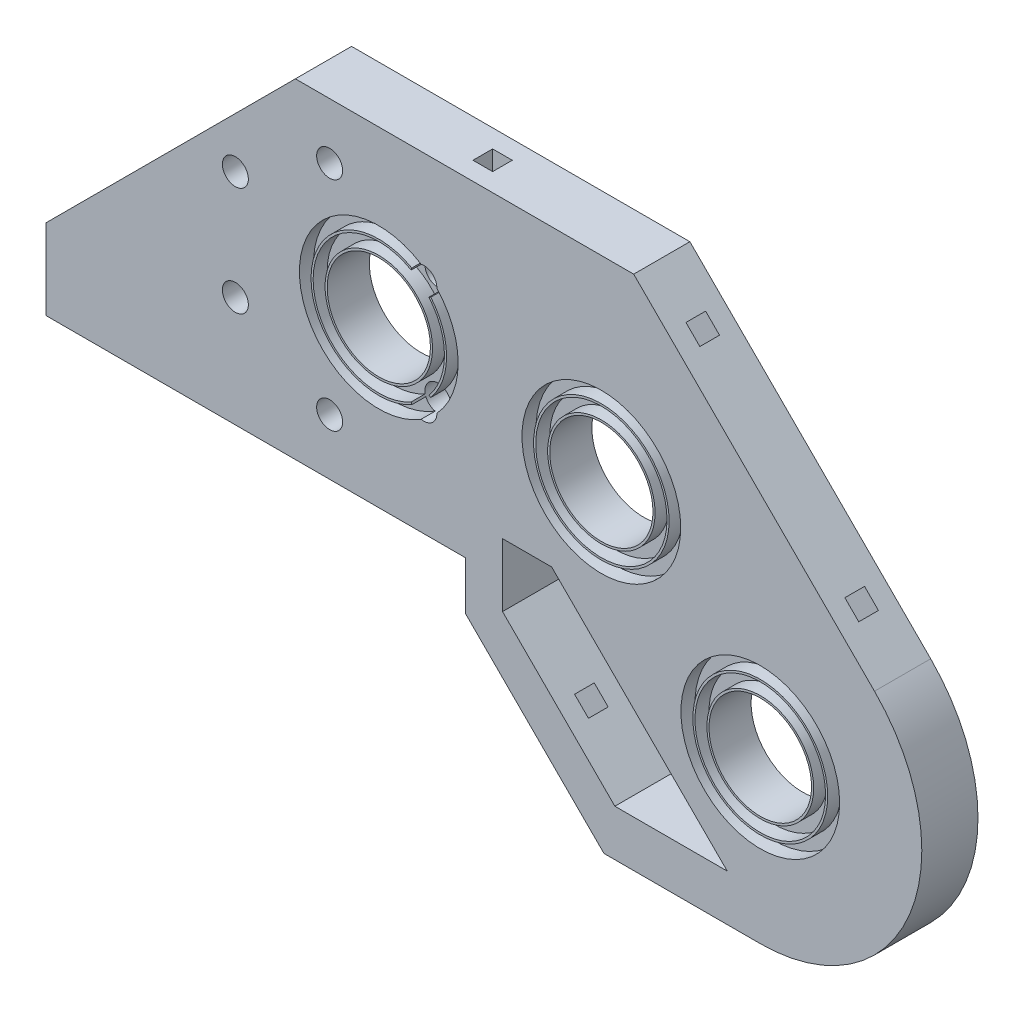
SolidWorks part; units mm, degrees
ref_plane "Plano frontal" through (0, 0, 0) normal (0, 0, 1) x (1, 0, 0)
ref_plane "Plano superior" through (0, 0, 0) normal (0, 1, 0) x (1, 0, 0)
ref_plane "Plano direito" through (0, 0, 0) normal (1, 0, 0) x (0, 0, -1)
sketch "Model" plane through (0, 0, 0) normal (0, 0, 1) x (1, 0, 0)
  line L0 (0, 0) -> (39, 0)
  line L1 (39, 0) -> (39.7, 0)
  line L2 (39.7, 0) -> (39.7, -6.8548)
  line L3 (0, 0) -> (0, 31.4419)
  line L4 (50.1111, 46.949) -> (15.5071, 46.949)
  line L5 (0, 31.4419) -> (15.5071, 46.949)
  line L6 (39.7, -6.8548) -> (52.4452, -19.6)
  line L7 (72, -15) -> (52, 5)
  line L8 (97.9635, 12.6635) -> (63.6779, 46.949)
  line L9 (50.1111, 46.949) -> (63.6779, 46.949)
  line L10 (52.4452, -19.6) -> (59.4452, -26.6)
  line L11 (81.7, -26.6) -> (59.4452, -26.6)
  line L12 (72, -15) -> (77, -20)
  line L13 (52, 5) -> (45, 5)
  line L14 (45, 5) -> (45, -4)
  line L15 (45, -4) -> (61, -20)
  line L16 (61, -20) -> (77, -20)
  circle A2 centre (59.0726, 19.0274) radius 7.35
  arc A5 (81.7, -26.6) -> (97.9635, 12.6635) centre (81.7, -3.6) ccw
  circle A6 centre (81.7, -3.6) radius 7.3
  circle A7 centre (6.9606, 15.731) radius 1.85
  circle A8 centre (6.9606, 31.231) radius 1.85
  circle A9 centre (20.384, 38.981) radius 1.85
  circle A10 centre (33.8074, 31.231) radius 1.85
  circle A11 centre (33.8074, 15.731) radius 1.85
  circle A12 centre (20.384, 7.981) radius 1.85
  circle A13 centre (27.384, 23.481) radius 7.35
sketch "Esboço2" plane through (0, 0, 0) normal (0, 0, 1) x (1, 0, 0)
  circle A15 centre (6.9606, 15.731) radius 3.3
  circle A16 centre (6.9606, 31.231) radius 3.3
  circle A17 centre (33.8074, 15.731) radius 3.3
  circle A18 centre (20.384, 38.981) radius 3.3
  circle A19 centre (33.8074, 31.231) radius 3.3
  circle A20 centre (20.384, 7.981) radius 3.3
sketch "Esboço3" plane through (0, 0, 0) normal (0, 0, 1) x (1, 0, 0)
  circle A3 centre (81.7, -3.6) radius 11.3
  circle A4 centre (59.0726, 19.0274) radius 11.3
  circle A14 centre (27.384, 23.481) radius 11.3
extrude "Ressalto-extrusão1" add sketch "Model" along normal blind 8
sketch "Esboço4" plane through (0, 0, 8) normal (0, 0, 1) x (1, 0, 0)
  circle A3 centre (81.7, -3.6) radius 11.3
  circle A4 centre (59.0726, 19.0274) radius 11.3
  circle A14 centre (27.384, 23.481) radius 11.3
extrude "Corte-extrusão1" cut sketch "Esboço3" along normal blind 2
extrude "Corte-extrusão2" cut sketch "Esboço4" against normal blind 2
extrude "Corte-extrusão4" cut sketch "Esboço2" along normal blind 2
sketch "Esboço7" plane through (55.3135, 55.3135, 0) normal (0.7071, 0.7071, 0) x (0, 0, -1)
  line L0 (0, -36.0727) -> (-8, -36.0727) construction
  line L2 (-4, -52.0727) -> (-4, -20.0727) construction
  line L3 (-5.4, -50.6727) -> (-2.6, -50.6727)
  line L4 (-5.4, -18.6727) -> (-2.6, -18.6727)
  line L5 (-5.4, -18.6727) -> (-5.4, -21.4727)
  line L6 (-5.4, -21.4727) -> (-2.6, -21.4727)
  line L7 (-2.6, -18.6727) -> (-2.6, -21.4727)
  line L8 (-5.4, -18.6727) -> (-2.6, -21.4727) construction
  line L9 (-5.4, -21.4727) -> (-2.6, -18.6727) construction
  line L10 (-2.6, -50.6727) -> (-2.6, -53.4727)
  line L11 (-5.4, -50.6727) -> (-2.6, -53.4727) construction
  line L12 (-5.4, -53.4727) -> (-2.6, -53.4727)
  line L13 (-5.4, -50.6727) -> (-5.4, -53.4727)
  line L14 (-5.4, -53.4727) -> (-2.6, -50.6727) construction
  line L15 (0, -60.3162) -> (0, -11.8291) construction
  line L16 (-8, -60.3162) -> (-8, -11.8291) construction
extrude "Corte-extrusão6" cut sketch "Esboço7" against normal blind 6
sketch "Esboço8" plane through (0, 46.949, 0) normal (0, 1, 0) x (1, 0, 0)
  line L0 (39.5925, 0) -> (39.5925, -8) construction
  line L1 (63.6779, 0) -> (15.5071, 0) construction
  line L2 (63.6779, -8) -> (15.5071, -8) construction
  line L4 (38.1925, -5.4) -> (40.9925, -5.4)
  line L5 (38.1925, -5.4) -> (38.1925, -2.6)
  line L6 (38.1925, -2.6) -> (40.9925, -2.6)
  line L7 (40.9925, -5.4) -> (40.9925, -2.6)
  line L8 (38.1925, -5.4) -> (40.9925, -2.6) construction
  line L9 (38.1925, -2.6) -> (40.9925, -5.4) construction
  point P6 (39.5925, -4)
extrude "Corte-extrusão7" cut sketch "Esboço8" against normal blind 6
sketch "Esboço10" plane through (16.4226, 16.4226, 0) normal (-0.7071, -0.7071, 0) x (0, 0, 1)
  line L0 (0, -46.8812) -> (8, -46.8812) construction
  line L1 (0, -32.9192) -> (0, -60.8431) construction
  line L2 (8, -32.9192) -> (8, -60.8431) construction
  line L4 (2.6, -45.4812) -> (5.4, -45.4812)
  line L5 (2.6, -45.4812) -> (2.6, -48.2812)
  line L6 (2.6, -48.2812) -> (5.4, -48.2812)
  line L7 (5.4, -45.4812) -> (5.4, -48.2812)
  line L8 (2.6, -45.4812) -> (5.4, -48.2812) construction
  line L9 (2.6, -48.2812) -> (5.4, -45.4812) construction
  point P6 (4, -46.8812)
extrude "Corte-extrusão9" cut sketch "Esboço10" against normal blind 6
sketch "Esboço11" plane through (0, 0, 6) normal (0, 0, 1) x (1, 0, 0)
  circle A0 centre (27.384, 23.481) radius 7.35 construction
  circle A1 centre (59.0726, 19.0274) radius 7.35 construction
  circle A2 centre (81.7, -3.6) radius 7.3 construction
  circle A3 centre (27.384, 23.481) radius 7.35
  circle A4 centre (59.0726, 19.0274) radius 7.35
  circle A5 centre (81.7, -3.6) radius 7.3
  circle A6 centre (27.384, 23.481) radius 7.65
  circle A7 centre (59.0726, 19.0274) radius 7.65
  circle A8 centre (81.7, -3.6) radius 7.6
  circle A9 centre (27.384, 23.481) radius 9.35
  circle A10 centre (59.0726, 19.0274) radius 9.35
  circle A11 centre (81.7, -3.6) radius 9.3
  circle A12 centre (27.384, 23.481) radius 9.65
  circle A13 centre (59.0726, 19.0274) radius 9.65
  circle A14 centre (81.7, -3.6) radius 9.6
  circle M1 centre (27.384, 23.481) radius 7.35
  arc M3 (33.4128, 13.9235) -> (35.6566, 15.7833) centre (33.8074, 15.731) cw
  arc M5 (35.6566, 31.1786) -> (33.4127, 33.0384) centre (33.8074, 31.231) cw
  dimension "D1" = 0.3
  dimension "D2" = 2
  dimension "D3" = 0.3
extrude "Ressalto-extrusão2" add sketch "Esboço11" along normal up to surface (2 mm away) contours A12 A9 M5 M3 | A6 M1 | A12 A9 M3 M5 | A7 A4 | A13 A10 | A14 A11 | A8 A5 up to face at (31.186, 23.481, 8)
sketch "Esboço13" plane through (0, 0, 8) normal (0, 0, 1) x (1, 0, 0)
  line L0 (0, 31.4419) -> (-20, 11.4419)
  line L1 (15.5071, 46.949) -> (0, 31.4419) construction
  line L2 (0, 0) -> (-20, 0)
  line L3 (0, 0) -> (-20, 0) construction
  line L4 (-20, 0) -> (-20, 11.4419)
  line L5 (0, 31.4419) -> (0, 0)
  dimension "D1" = 20
  dimension "D2" = 11.4419
extrude "Ressalto-extrusão3" add sketch "Esboço13" against normal up to surface (8 mm away) up to face at (31.6486, 23.481, 0)
sketch "Esboço6" plane through (0, 0, 0) normal (0, -1, 0) x (1, 0, 0)
  line L0 (39.7, 8) -> (39.7, 0) construction
  line L1 (4.7, 4) -> (-14.3, 4) construction
  line L2 (4.7, 4) -> (23.7, 4) construction
  circle A0 centre (4.7, 4) radius 1.5
  circle A1 centre (23.7, 4) radius 1.5
  circle A2 centre (-14.3, 4) radius 1.5
  dimension "D1" = 19
  dimension "D2" = 16
extrude "Corte-extrusão5" cut sketch "Esboço6" against normal blind 10
sketch "Esboço14" plane through (0, 0, 8) normal (0, 0, 1) x (1, 0, 0)
  line L0 (-3.2, 8) -> (-3.2, 29.2319) construction
  line L1 (-3.2, 8) -> (-3.2, 29.2319) construction
  line L2 (-3.2, 28.2419) -> (-3.2, 0)
  line L3 (15.5071, 46.949) -> (-20, 11.4419) construction
  line L4 (-20, 0) -> (39.7, 0) construction
  line L5 (-3.2, 0) -> (-20, 0)
  line L6 (-20, 0) -> (-20, 11.4419)
  line L7 (-20, 11.4419) -> (-3.2, 28.2419)
